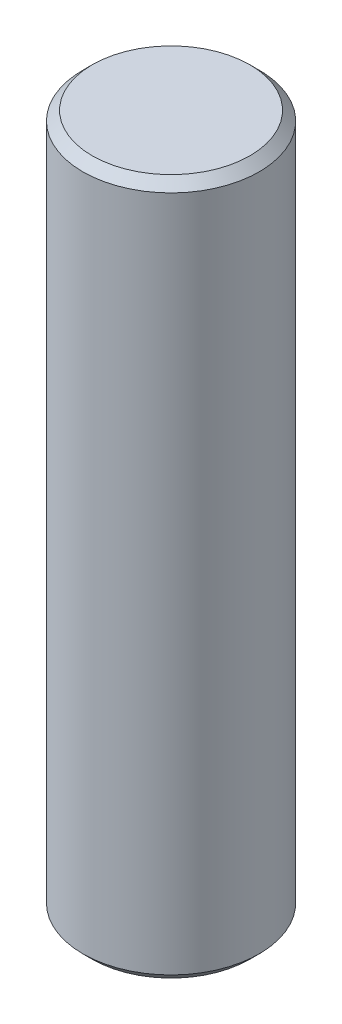
SolidWorks part; units mm, degrees
ref_plane "Front Plane" through (0, 0, 0) normal (0, 0, 1) x (1, 0, 0)
ref_plane "Top Plane" through (0, 0, 0) normal (0, 1, 0) x (1, 0, 0)
ref_plane "Right Plane" through (0, 0, 0) normal (1, 0, 0) x (0, 0, -1)
sketch "Sketch2" plane through (0, 0, 0) normal (0, 1, 0) x (1, 0, 0)
  circle A0 centre (0, 0) radius 4.826
  dimension "D1" = 9.652
extrude "Boss-Extrude1" add sketch "Sketch2" along normal mid plane 38.1
chamfer "Chamfer1" distance 0.508 angle 45 2 edges at (0, -19.05, 4.826) (0, 19.05, 4.826)
